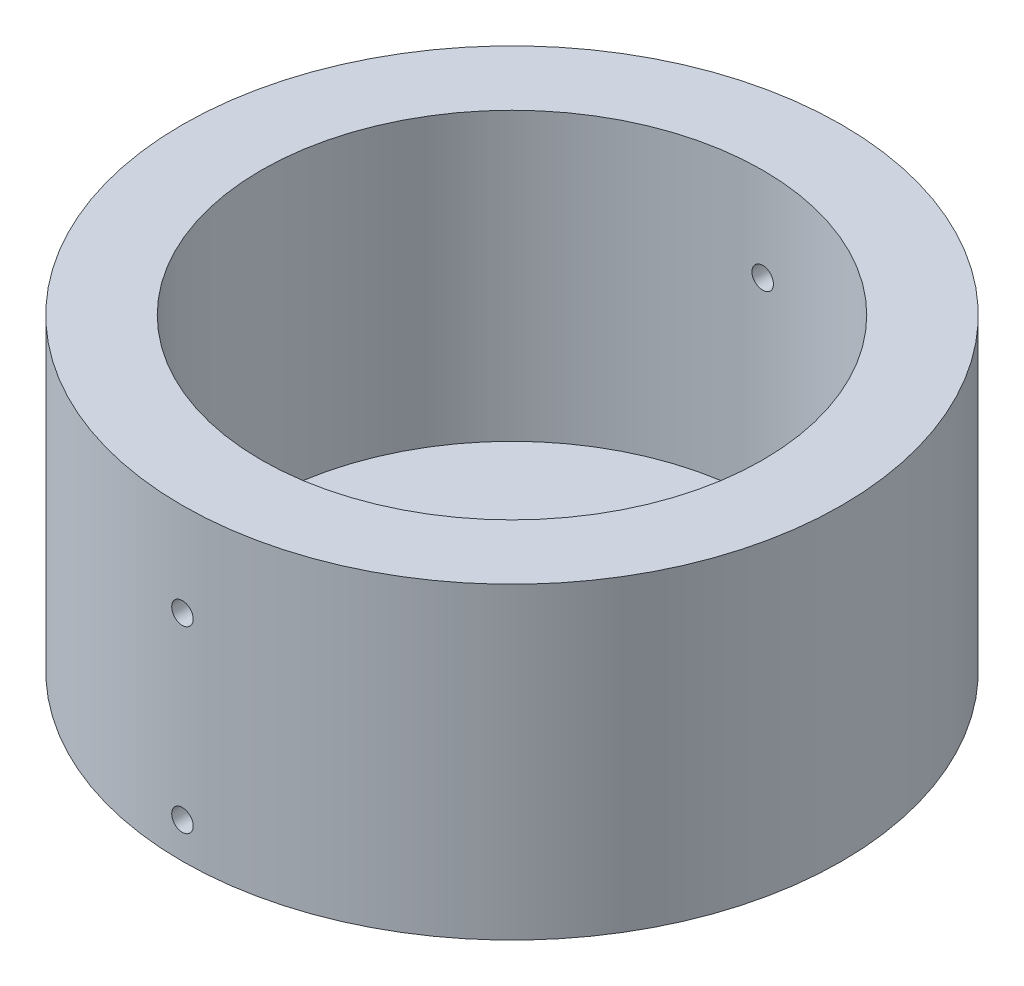
SolidWorks part; units mm, degrees
material "1060 Alloy"
ref_plane "Front Plane" through (0, 0, 0) normal (0, 0, 1) x (1, 0, 0)
ref_plane "Top Plane" through (0, 0, 0) normal (0, 1, 0) x (1, 0, 0)
ref_plane "Right Plane" through (0, 0, 0) normal (1, 0, 0) x (0, 0, -1)
sketch "Sketch1" plane through (0, 0, 0) normal (0, 1, 0) x (1, 0, 0)
  circle A0 centre (0, 0) radius 46
  circle A1 centre (0, 0) radius 3
  circle A3 centre (0, 9.5) radius 1.4
  circle A4 centre (8.2272, 4.75) radius 1.4
  circle A5 centre (8.2272, -4.75) radius 1.4
  circle A6 centre (0, -9.5) radius 1.4
  circle A7 centre (-8.2272, -4.75) radius 1.4
  circle A8 centre (-8.2272, 4.75) radius 1.4
  point P20 (0, 0)
  dimension "D1" = 92
  dimension "D2" = 6
  dimension "D4" = 2.8
  dimension "D5" = 6
extrude "Boss-Extrude1" add sketch "Sketch1" along normal blind 3
ref_plane "Plane2" through (0, 0, 46) normal (0, 0, 1) x (1, 0, 0)
ref_plane "Plane3" through (0, 0, -46) normal (0, 0, 1) x (1, 0, 0)
sketch "Sketch6" plane through (0, 0, -46) normal (0, 0, 1) x (1, 0, 0)
  line L0 (0, 0) -> (0, 1.5) construction
  line L1 (-46, 0) -> (46, 0) construction
  circle A0 centre (0, 1.5) radius 1
  dimension "D2" = 2
  dimension "D1" = 1.5
extrude "Cut-Extrude2" cut sketch "Sketch6" along normal blind 3
sketch "Sketch7" plane through (0, 3, 0) normal (0, 1, 0) x (1, 0, 0)
  circle A0 centre (0, 0) radius 46
  circle A1 centre (0, 0) radius 35
  dimension "D1" = 70
extrude "Boss-Extrude2" add sketch "Sketch7" along normal blind 40
sketch "Sketch8" plane through (0, 0, 46) normal (0, 0, 1) x (1, 0, 0)
  line L0 (0, 0) -> (0, 30) construction
  circle A0 centre (0, 30) radius 1.5
  dimension "D2" = 3
  dimension "D1" = 30
extrude "Cut-Extrude3" cut sketch "Sketch8" against normal blind 108
sketch "Sketch9" plane through (0, 0, 0) normal (0, 0, 1) x (1, 0, 0)
  line L0 (0, 0) -> (0, 5) construction
  circle A0 centre (0, 5) radius 1.5
  dimension "D2" = 3
  dimension "D1" = 5
extrude "Cut-Extrude4" cut sketch "Sketch9" against normal through all and the other way through all
